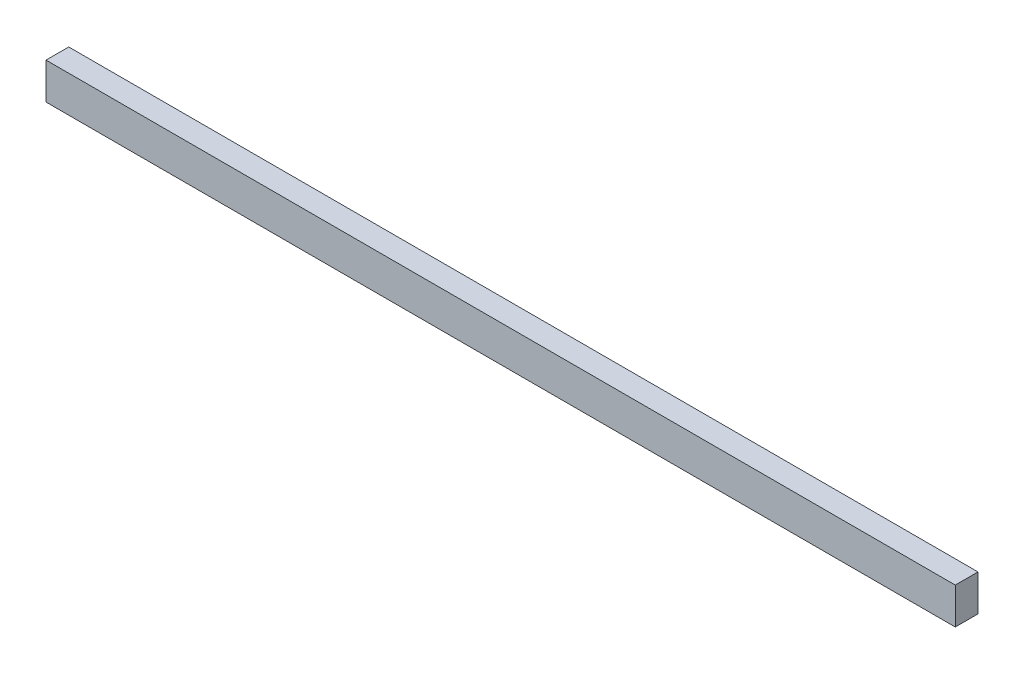
SolidWorks part; units mm, degrees
ref_plane "Front Plane" through (0, 0, 0) normal (0, 0, 1) x (1, 0, 0)
ref_plane "Top Plane" through (0, 0, 0) normal (0, 1, 0) x (1, 0, 0)
ref_plane "Right Plane" through (0, 0, 0) normal (1, 0, 0) x (0, 0, -1)
sketch "Sketch1" plane through (0, 0, 0) normal (0, 0, 1) x (1, 0, 0)
  line L1 (0, 0) -> (254, 0)
  line L2 (0, 0) -> (0, 10.16)
  line L3 (0, 10.16) -> (254, 10.16)
  line L4 (254, 0) -> (254, 10.16)
  dimension "D1" = 254
  dimension "D2" = 10.16
extrude "Boss-Extrude1" add sketch "Sketch1" along normal blind 6.35 contours L1 L4 L3 L2
